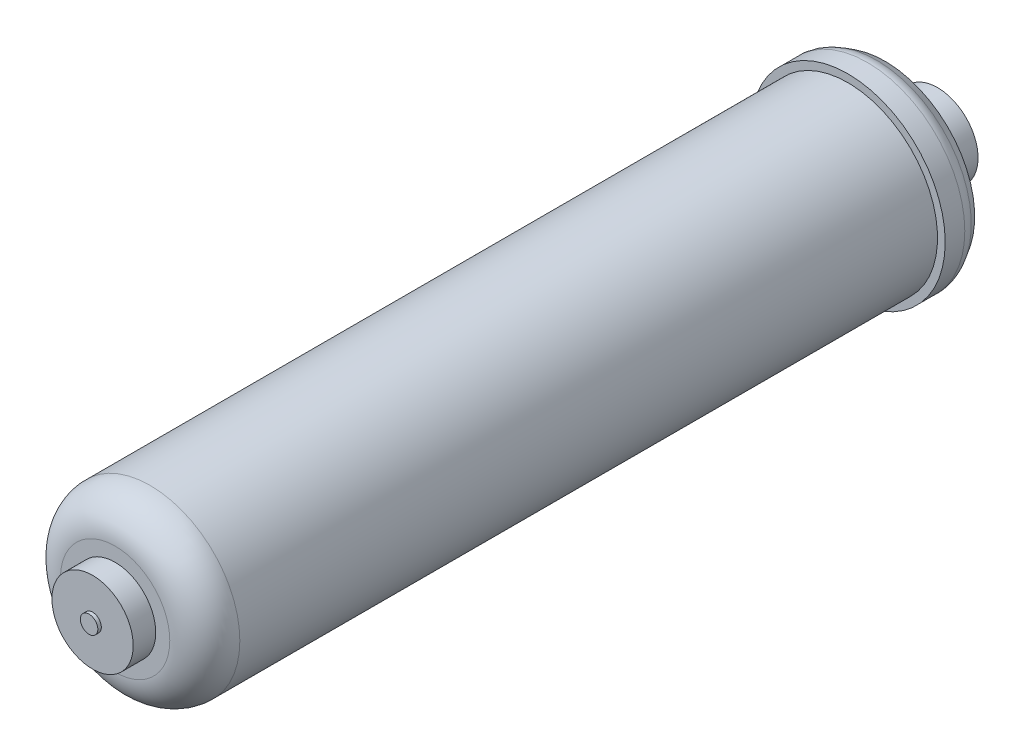
SolidWorks part; units mm, degrees
ref_plane "Front Plane" through (0, 0, 0) normal (0, 0, 1) x (1, 0, 0)
ref_plane "Top Plane" through (0, 0, 0) normal (0, 1, 0) x (1, 0, 0)
ref_plane "Right Plane" through (0, 0, 0) normal (1, 0, 0) x (0, 0, -1)
sketch "Sketch1" plane through (0, 0, 0) normal (1, 0, 0) x (0, 0, -1)
  line L0 (0, 0) -> (0, 3.175)
  line L1 (0, 3.175) -> (-1.27, 3.175)
  line L2 (-1.27, 3.175) -> (-1.27, 14.732)
  line L3 (-1.27, 14.732) -> (-9.398, 14.732)
  line L4 (-9.398, 14.732) -> (-20.32, 32.5551)
  line L5 (-24.892, 35.306) -> (-33.7566, 35.306)
  line L6 (-33.7566, 35.306) -> (-33.7566, 32.512)
  line L7 (-33.7566, 32.512) -> (-299.4152, 32.512)
  line L8 (-299.4152, 32.512) -> (-299.4152, 14.732)
  line L9 (-299.4152, 14.732) -> (-307.594, 14.732)
  line L10 (-307.594, 14.732) -> (-307.594, 3.175)
  line L11 (-307.594, 3.175) -> (-308.864, 3.175)
  line L12 (-308.864, 3.175) -> (-308.864, 0)
  line L13 (0, 0) -> (-438.0055, 0) construction
  line L14 (0, 0) -> (-308.864, 0)
  line L15 (-20.32, 32.5551) -> (-24.892, 35.306)
  dimension "D1" = 306.324
  dimension "D2" = 8.1788
  dimension "D3" = 8.128
  dimension "D4" = 273.8374
  dimension "D5" = 65.024
  dimension "D6" = 70.612
  dimension "D7" = 6.35
  dimension "D8" = 14.732
  dimension "D9" = 6.35
  dimension "D10" = 29.464
  dimension "D11" = 1.27
  dimension "D12" = 1.27
  dimension "D13" = 10.922
  dimension "D14" = 4.572
  dimension "D15" = 121.5
revolve "Revolve1" add sketch "Sketch1" angle 360 about L13
fillet "Fillet1" radius 12.7 1 edges at (-32.512, 0, 299.4152)
fillet "Fillet2" radius 6.35 1 edges at (-35.306, 0, 24.892)
